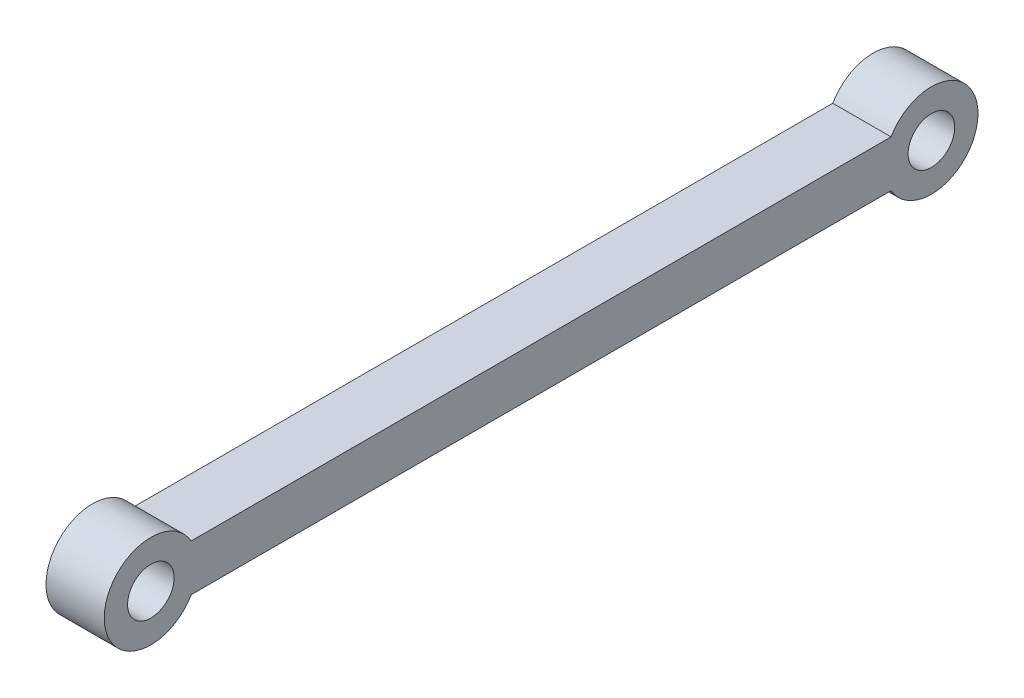
SolidWorks part; units mm, degrees
ref_plane "Front Plane" through (0, 0, 0) normal (0, 0, 1) x (1, 0, 0)
ref_plane "Top Plane" through (0, 0, 0) normal (0, 1, 0) x (1, 0, 0)
ref_plane "Right Plane" through (0, 0, 0) normal (1, 0, 0) x (0, 0, -1)
sketch "Sketch1" plane through (0, 0, 0) normal (1, 0, 0) x (0, 0, -1)
  line L1 (-15.0179, -2) -> (15.0179, -2)
  line L3 (-15.0179, 0) -> (15.0179, 0)
  arc A0 (-15.0179, 0) -> (-15.0179, -2) centre (-16.75, -1) ccw
  arc A1 (15.0179, -2) -> (15.0179, 0) centre (16.75, -1) ccw
  circle A2 centre (-16.75, -1) radius 1
  circle A3 centre (16.75, -1) radius 1
  point P0 (0, 0)
  point P1 (0, 0)
  point P3 (0, -2)
  dimension "D2" = 4
  dimension "D4" = 2
  dimension "D3" = 2
  dimension "D1" = 33.5
extrude "Boss-Extrude1" add sketch "Sketch1" along normal mid plane 2.5
